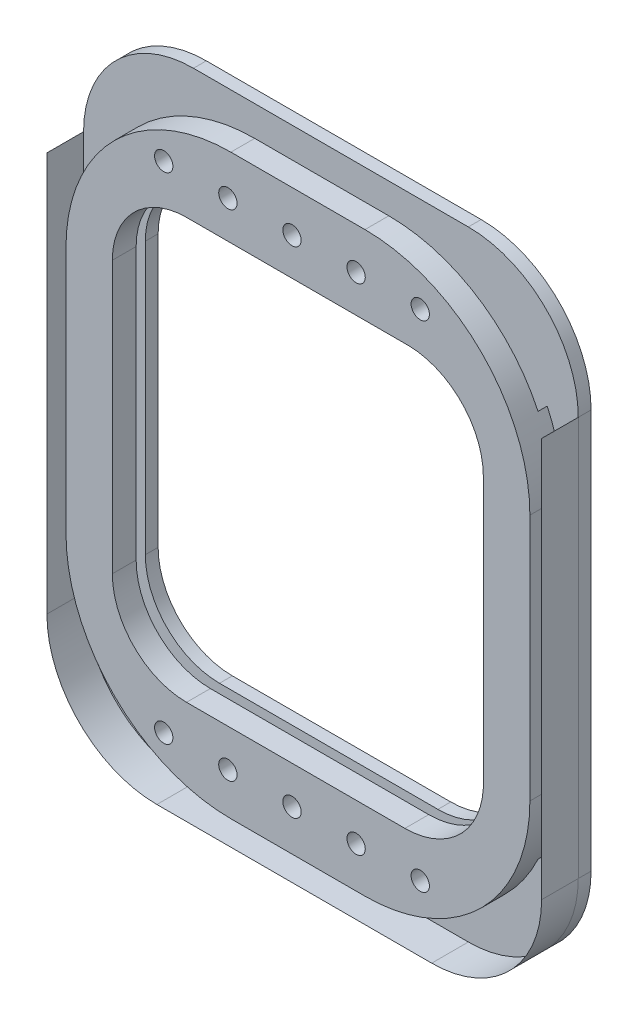
SolidWorks part; units mm, degrees
ref_plane "Front Plane" through (0, 0, 0) normal (0, 0, 1) x (1, 0, 0)
ref_plane "Top Plane" through (0, 0, 0) normal (0, 1, 0) x (1, 0, 0)
ref_plane "Right Plane" through (0, 0, 0) normal (1, 0, 0) x (0, 0, -1)
sketch "Sketch1" plane through (0, 0, 0) normal (0, 0, 1) x (1, 0, 0)
  line L53 (241.5433, 205.3413) -> (246.9652, 204.9327)
  line L72 (-6.9957, 198.2293) -> (-6.9957, -78.6307)
  line L73 (35.8033, 153.9063) -> (35.8033, -34.3077)
  line L74 (69.2043, 274.4293) -> (259.7043, 274.4293)
  line L75 (335.9043, 198.2293) -> (335.9043, -78.6307)
  line L76 (259.7043, -154.8307) -> (69.2043, -154.8307)
  line L77 (87.2383, 205.3413) -> (241.5433, 205.3413)
  line L78 (35.8033, 153.9063) -> (35.8033, -34.3077)
  line L79 (87.2383, -85.7427) -> (238.612, -85.7427)
  line L80 (292.9783, 152.6781) -> (292.9783, -34.3077)
  line L81 (87.2383, -85.7427) -> (238.612, -85.7427)
  line L82 (292.9783, -34.3077) -> (292.9783, 152.6781)
  line L83 (241.5433, 205.3413) -> (87.2383, 205.3413)
  line L84 (-6.9957, 198.2293) -> (-6.9957, -78.6307)
  line L85 (69.2043, -154.8307) -> (259.7043, -154.8307)
  line L86 (335.9043, -78.6307) -> (335.9043, 198.2293)
  line L87 (259.7043, 274.4293) -> (69.2043, 274.4293)
  arc A32 (35.8033, -34.3077) -> (87.2383, -85.7427) centre (87.2383, -34.3077) ccw
  arc A33 (238.612, -85.7427) -> (292.9783, -34.3077) centre (238.612, -31.2928) ccw
  arc A34 (292.9783, 152.6781) -> (241.5433, 205.3413) centre (240.3004, 152.6781) ccw
  arc A35 (87.2383, 205.3413) -> (35.8033, 153.9063) centre (87.2383, 153.9063) ccw
  arc A36 (-6.9957, -78.6307) -> (69.2043, -154.8307) centre (69.2043, -78.6307) ccw
  arc A37 (259.7043, -154.8307) -> (335.9043, -78.6307) centre (259.7043, -78.6307) ccw
  arc A38 (335.9043, 198.2293) -> (259.7043, 274.4293) centre (259.7043, 198.2293) ccw
  arc A39 (69.2043, 274.4293) -> (-6.9957, 198.2293) centre (69.2043, 198.2293) ccw
  point P7 (-1548.8445, 807.057)
  point P171 (69.2043, 274.4293)
  point P172 (259.7043, 274.4293)
  point P173 (335.9043, 198.2293)
  point P174 (335.9043, -78.6307)
  point P175 (87.2383, 205.3413)
  point P176 (241.5433, 205.3413)
  point P181 (292.9783, 152.6781)
  point P182 (292.9783, -34.3077)
  point P183 (241.5433, -85.7427)
  point P184 (87.2383, -85.7427)
  point P185 (35.8033, -34.3077)
  point P186 (35.8033, 153.9063)
  point P187 (259.7043, -154.8307)
  point P188 (69.2043, -154.8307)
  point P200 (-6.9957, -78.6307)
  point P202 (-6.9957, 198.2293)
extrude "Boss-Extrude1" add sketch "Sketch1" along normal blind 63.5 contours L74 A39 L72 A36 L76 A37 L75 A38 A35 L77 A34 L80 A33 L79 A32 L73
sketch "Sketch3" plane through (0, -85.7427, 0) normal (0, 1, 0) x (1, 0, 0)
  line L0 (87.2383, -5.08) -> (238.612, -5.08)
  line L1 (87.2383, -63.5) -> (87.2383, 0) construction
  line L2 (238.612, -63.5) -> (238.612, 0) construction
  line L3 (87.2383, -15.24) -> (238.612, -15.24)
  point P4 (238.612, -15.24)
  point P5 (238.612, -5.08)
  point P6 (87.2383, -5.08)
  point P10 (87.2383, -15.24)
  dimension "D1" = 5.08
  dimension "D2" = 10.16
  dimension "D3" = 10.16
ref_plane "Plane1" through (0, 0, 10.16) normal (0, 0, 1) x (1, 0, 0)
sketch "Sketch4" plane through (0, 0, 10.16) normal (0, 0, 1) x (1, 0, 0)
  line L0 (164.4543, 274.4293) -> (164.4543, -154.8307) construction
  line L1 (69.2043, 274.4293) -> (259.7043, 274.4293) construction
  line L2 (259.7043, -154.8307) -> (69.2043, -154.8307) construction
  line L3 (87.2383, 205.3413) -> (241.5433, 205.3413) construction
  line L4 (35.8033, 153.9063) -> (35.8033, -34.3077) construction
  line L5 (-6.9957, 198.2293) -> (-6.9957, -78.6307) construction
  line L6 (335.9043, 198.2293) -> (335.9043, -78.6307) construction
  line L7 (292.9783, 152.6781) -> (292.9783, -34.3077) construction
  line L8 (14.5298, 274.4293) -> (14.5298, -154.8307)
  line L9 (200.0789, -104.0307) -> (128.8298, -104.0307) construction
  line L11 (200.0789, 223.6293) -> (128.8298, 223.6293) construction
  line L12 (14.5298, 10.2693) -> (14.5298, 109.3293) construction
  line L13 (314.3789, -104.0307) -> (14.5298, 223.6293) construction
  line L14 (314.3789, 223.6293) -> (14.5298, -104.0307) construction
  line L16 (314.3789, 274.4293) -> (314.3789, -154.8307)
  line L17 (314.3789, 274.4293) -> (14.5298, 274.4293)
  line L18 (14.5298, -154.8307) -> (314.3789, -154.8307)
  arc A0 (200.0789, 223.6293) -> (314.3789, 109.3293) centre (200.0789, 109.3293) cw construction
  arc A1 (200.0789, -104.0307) -> (314.3789, 10.2693) centre (200.0789, 10.2693) ccw construction
  arc A2 (128.8298, -104.0307) -> (14.5298, 10.2693) centre (128.8298, 10.2693) cw construction
  arc A3 (14.5298, 109.3293) -> (128.8298, 223.6293) centre (128.8298, 109.3293) cw construction
  point P6 (164.4543, -120.2867)
  point P7 (14.4673, 59.7993)
  point P8 (164.4543, 236.3293)
  point P9 (314.4331, 59.7807)
  point P10 (-6.9957, 59.7993)
  point P13 (164.3908, 205.3413)
  point P14 (335.9043, 59.7993)
  point P15 (35.8033, 59.7993)
  point P20 (292.9783, 59.1852)
  point P23 (164.4543, 59.7993)
  dimension "D6" = 114.3
  dimension "D1" = 38.1
  dimension "D2" = 34.544
  dimension "D3" = 42.926
  dimension "D4" = 21.463
  dimension "D5" = 21.463
  dimension "D7" = 50.8
  dimension "D8" = 50.8
extrude "Cut-Extrude2" cut sketch "Sketch4" along normal blind 5.08 and the other way blind 1.27
ref_plane "Plane2" through (0, 0, 8.89) normal (0, 0, 1) x (1, 0, 0)
sketch "Sketch9" plane through (0, 0, 8.89) normal (0, 0, 1) x (1, 0, 0)
  line L0 (-6.9957, 198.2293) -> (-6.9957, -78.6307) construction
  line L1 (335.9043, 198.2293) -> (335.9043, -78.6307) construction
  line L2 (69.2043, -154.8307) -> (259.7043, -154.8307)
  line L4 (259.7043, -154.8307) -> (69.2043, -154.8307) construction
  line L6 (117.9723, -140.2857) -> (210.9363, -140.2857)
  line L7 (3.6723, -25.9857) -> (3.6723, 145.5844)
  line L8 (117.9723, 259.8844) -> (210.9363, 259.8844)
  line L9 (325.2363, -25.9857) -> (325.2363, 145.5844)
  line L10 (3.6723, -140.2857) -> (12.4013, -129.4229) construction
  line L11 (3.6723, 259.8844) -> (12.4013, 249.0216) construction
  line L12 (335.9043, -78.6307) -> (335.9043, 198.2293)
  line L13 (259.7043, 274.4293) -> (69.2043, 274.4293)
  line L14 (-6.9957, 198.2293) -> (-6.9957, -78.6307)
  line L16 (316.5074, 249.0216) -> (325.2363, 259.8844) construction
  line L17 (316.5074, -129.4229) -> (325.2363, -140.2857) construction
  arc A0 (210.9363, -140.2857) -> (325.2363, -25.9857) centre (210.9363, -25.9857) ccw
  arc A1 (117.9723, -140.2857) -> (3.6723, -25.9857) centre (117.9723, -25.9857) cw
  arc A2 (3.6723, 145.5844) -> (117.9723, 259.8844) centre (117.9723, 145.5844) cw
  arc A3 (210.9363, 259.8844) -> (325.2363, 145.5844) centre (210.9363, 145.5844) cw
  arc A4 (259.7043, -154.8307) -> (335.9043, -78.6307) centre (259.7043, -78.6307) ccw construction
  arc A5 (259.7043, -154.8307) -> (335.9043, -78.6307) centre (259.7043, -78.6307) ccw
  arc A6 (335.9043, 198.2293) -> (259.7043, 274.4293) centre (259.7043, 198.2293) ccw
  arc A7 (69.2043, 274.4293) -> (-6.9957, 198.2293) centre (69.2043, 198.2293) ccw
  arc A8 (-6.9957, -78.6307) -> (69.2043, -154.8307) centre (69.2043, -78.6307) ccw
  arc A9 (-6.9957, -78.6307) -> (69.2043, -154.8307) centre (69.2043, -78.6307) ccw construction
  point P0 (164.4543, 259.8844)
  point P1 (325.2363, 59.7993)
  point P2 (164.4543, -136.6443)
  point P3 (-6.9957, 59.7993)
  point P4 (3.6723, 59.7993)
  point P15 (164.4543, 59.7993)
  dimension "D3" = 114.3
  dimension "D1" = 10.668
  dimension "D2" = 10.668
extrude "Cut-Extrude4" cut sketch "Sketch9" along normal blind 25.4
sketch "Sketch10" plane through (0, 0, 0) normal (0, 0, 1) x (1, 0, 0)
  line L0 (69.2043, 274.4293) -> (259.7043, 274.4293) construction
  circle A0 centre (249.2393, 231.2493) radius 6.35
  dimension "D2" = 12.7
  dimension "D1" = 43.18
extrude "Cut-Extrude5" cut sketch "Sketch10" along normal blind 119.38 and the other way through all
pattern_linear "LPattern1" count 5 spacing 44.45 along (-1, 0, 0) of "Cut-Extrude5"
ref_plane "Plane4" through (0, 59.69, 0) normal (0, 1, 0) x (1, 0, 0)
mirror "Mirror1" about plane through (0, 59.69, 0) normal (0, 1, 0) of "Cut-Extrude5", "LPattern1"
ref_plane "Plane5" through (0, 0, 31.75) normal (0, 0, -1) x (-1, 0, 0)
sketch "Sketch11" plane through (0, 0, 31.75) normal (0, 0, -1) x (-1, 0, 0)
  line L1 (-346.4397, 288.4308) -> (15.5601, 288.4308)
  line L2 (-346.4397, 288.4308) -> (-346.4397, -164.8903)
  line L3 (-346.4397, -164.8903) -> (15.5601, -164.8903)
  line L4 (15.5601, 288.4308) -> (15.5601, -164.8903)
extrude "Cut-Extrude6" cut sketch "Sketch11" against normal through all
sketch "Sketch12" plane through (0, 0, 8.89) normal (0, 0, 1) x (1, 0, 0)
  line L0 (-6.9957, 198.2293) -> (-6.9957, -78.6307)
  line L1 (69.2043, -154.8307) -> (259.7043, -154.8307)
  line L2 (335.9043, -78.6307) -> (335.9043, 198.2293)
  arc A0 (-6.9957, -78.6307) -> (69.2043, -154.8307) centre (69.2043, -78.6307) ccw
  arc A1 (259.7043, -154.8307) -> (335.9043, -78.6307) centre (259.7043, -78.6307) ccw
  arc A2 (259.7043, -154.8307) -> (335.9043, -78.6307) centre (259.7043, -78.6307) ccw construction
surface "Surface-Extrude1" sketch "Sketch12" parameters "D1"=25.4
sketch "Sketch13" plane through (0, 0, 0) normal (0, 0, -1) x (-1, 0, 0)
  circle A0 centre (-249.2442, 231.2509) radius 6.3551
  point P0 (0, 0)
extrude "Boss-Extrude2" add sketch "Sketch13" against normal blind 7.62
sketch "Sketch14" plane through (0, 0, 0) normal (0, 0, -1) x (-1, 0, 0)
  line L0 (-255.8482, 231.2509) -> (-242.6402, 231.2509)
  arc A0 (-242.6402, 231.2509) -> (-255.8482, 231.2509) centre (-249.2442, 231.2509) ccw
revolve "Revolve1" add sketch "Sketch14" angle 180 about L0
pattern_linear "LPattern2" count 5 spacing 44.45 along (-1, 0, 0) of "Revolve1", "Boss-Extrude2"
pattern_linear "LPattern3" count 2 spacing 342.9 along (0, -1, 0) of "Revolve1", "Boss-Extrude2", "LPattern2"
